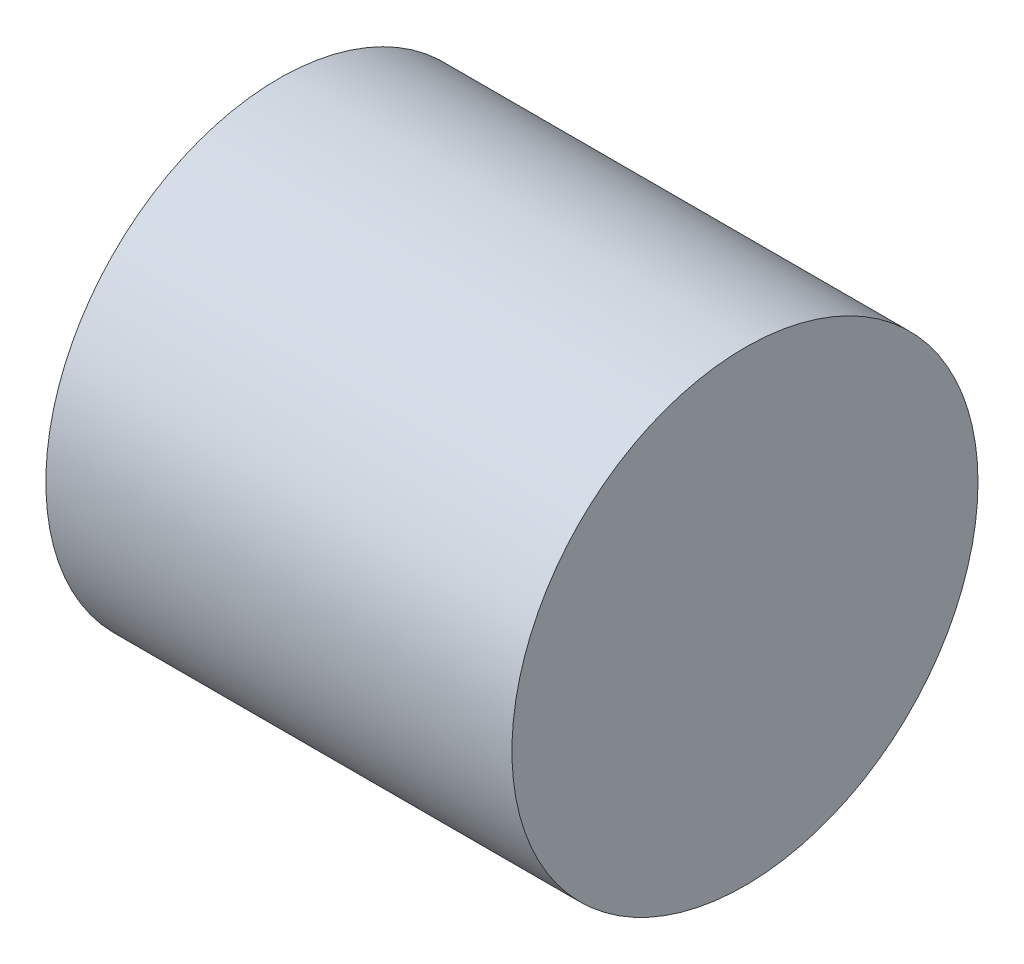
SolidWorks part; units mm, degrees
ref_plane "Front Plane" through (0, 0, 0) normal (0, 0, 1) x (1, 0, 0)
ref_plane "Top Plane" through (0, 0, 0) normal (0, 1, 0) x (1, 0, 0)
ref_plane "Right Plane" through (0, 0, 0) normal (1, 0, 0) x (0, 0, -1)
sketch "Sketch2" plane through (0, 0, 0) normal (1, 0, 0) x (0, 0, -1)
  circle A0 centre (0, 0) radius 5
  dimension "D1" = 10
extrude "Boss-Extrude1" add sketch "Sketch2" along normal blind 10
